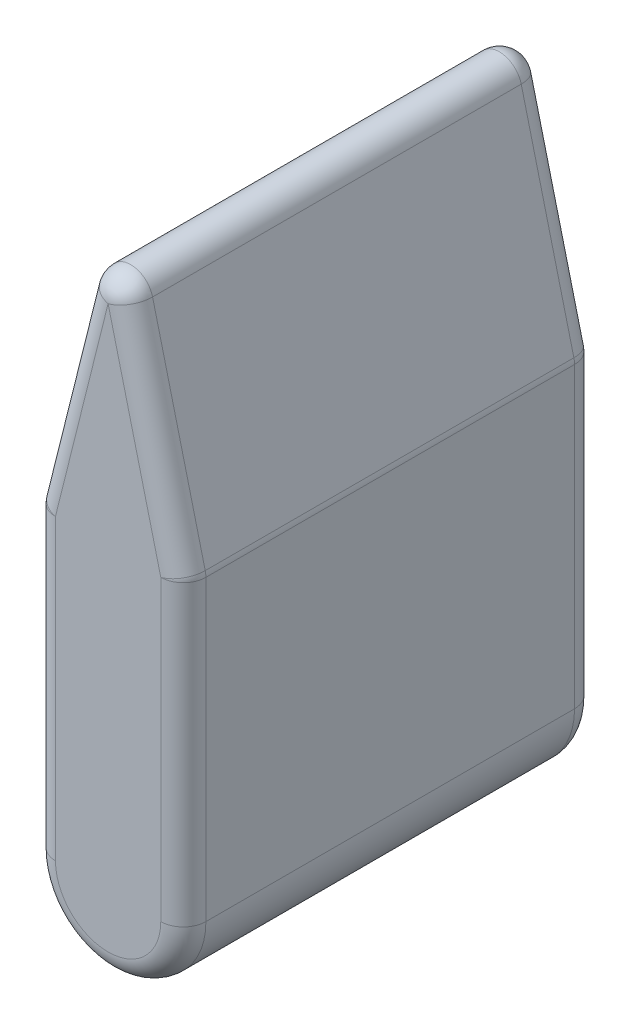
SolidWorks part; units mm, degrees
ref_plane "Front Plane" through (0, 0, 0) normal (0, 0, 1) x (1, 0, 0)
ref_plane "Top Plane" through (0, 0, 0) normal (0, 1, 0) x (1, 0, 0)
ref_plane "Right Plane" through (0, 0, 0) normal (1, 0, 0) x (0, 0, -1)
sketch "Sketch1" plane through (0, 0, 0) normal (0, 0, 1) x (1, 0, 0)
  line L0 (-10, 0) -> (-10, 40)
  line L1 (-10, 40) -> (0, 80)
  line L2 (0, 80) -> (10, 40)
  line L3 (10, 40) -> (10, 0)
  arc A1 (-10, 0) -> (10, 0) centre (0, 0) ccw
  arc A2 (10, 0) -> (-10, 0) centre (0, 0) ccw construction
  point P1 (0, 0)
  dimension "D1" = 10
  dimension "D2" = 40
  dimension "D3" = 40
extrude "Boss-Extrude1" add sketch "Sketch1" along normal mid plane 55
fillet "Fillet1" radius 3 13 edges at (10, 20, -27.5) (5, 60, -27.5) (-5, 60, -27.5) (-10, 20, -27.5) (0, -10, -27.5) (-10, 20, 27.5) (-5, 60, 27.5) (5, 60, 27.5) (10, 20, 27.5) (0, -10, 27.5) (10, 40, 0) (-10, 40, 0) (0, 80, 0)
